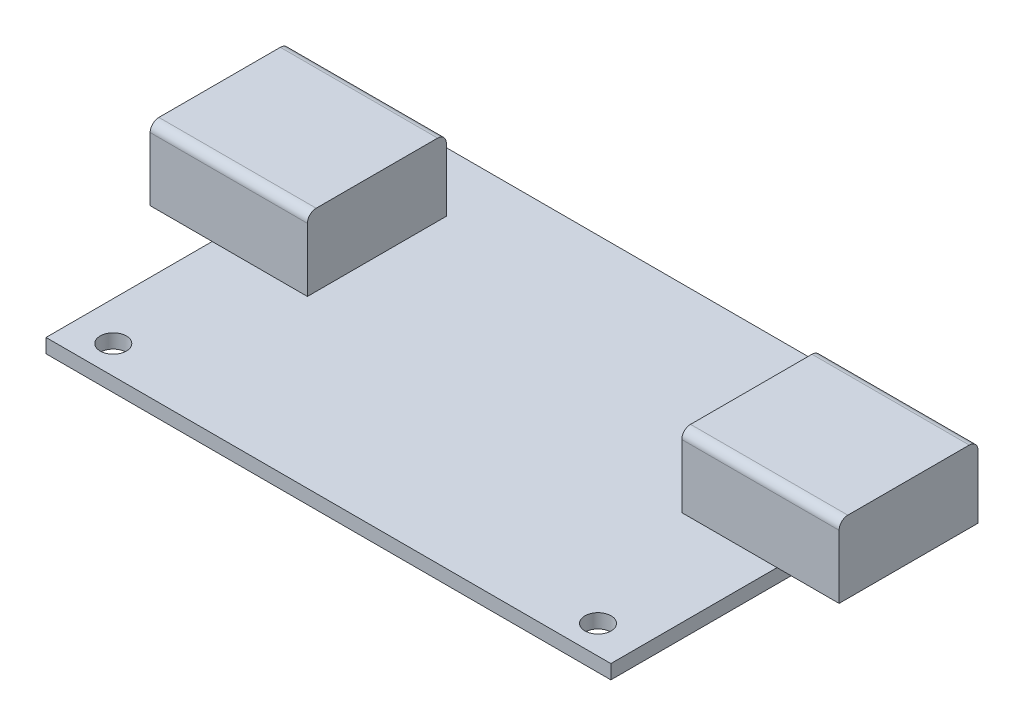
SolidWorks part; units mm, degrees
ref_plane "Front Plane" through (0, 0, 0) normal (0, 0, 1) x (1, 0, 0)
ref_plane "Top Plane" through (0, 0, 0) normal (0, 1, 0) x (1, 0, 0)
ref_plane "Right Plane" through (0, 0, 0) normal (1, 0, 0) x (0, 0, -1)
sketch "Sketch1" plane through (0, 0, 0) normal (0, 1, 0) x (1, 0, 0)
  line L0 (-27.875, -17.61) -> (27.605, -17.61) construction
  line L1 (-32.325, -20.86) -> (32.325, -20.86)
  line L2 (-32.325, -20.86) -> (-32.325, 20.86)
  line L3 (-32.325, 20.86) -> (32.325, 20.86)
  line L4 (32.325, -20.86) -> (32.325, 20.86)
  line L5 (-32.325, -20.86) -> (32.325, 20.86) construction
  line L6 (-32.325, 20.86) -> (32.325, -20.86) construction
  line L7 (-29.325, 17.01) -> (28.875, 17.01) construction
  circle A0 centre (27.605, -17.61) radius 1.5
  circle A1 centre (-27.875, -17.61) radius 1.5
  circle A2 centre (28.875, 17.01) radius 1.5
  circle A3 centre (-29.325, 17.01) radius 1.5
  point P0 (0, 0)
  dimension "D9" = 3
  dimension "D1" = 64.65
  dimension "D2" = 41.72
  dimension "D3" = 4.72
  dimension "D4" = 3.25
  dimension "D5" = 4.45
  dimension "D6" = 3.45
  dimension "D7" = 3
  dimension "D8" = 3.85
extrude "Boss-Extrude1" add sketch "Sketch1" along normal blind 1.62
sketch "Sketch2" plane through (0, 1.62, 0) normal (0, 1, 0) x (1, 0, 0)
  line L0 (32.325, 20.86) -> (-32.325, 20.86) construction
  line L1 (-39.425, -1.84) -> (-21.425, -1.84)
  line L2 (-39.425, -1.84) -> (-39.425, 14.06)
  line L3 (-39.425, 14.06) -> (-21.425, 14.06)
  line L4 (-21.425, -1.84) -> (-21.425, 14.06)
  line L5 (-39.425, -1.84) -> (-21.425, 14.06) construction
  line L6 (-39.425, 14.06) -> (-21.425, -1.84) construction
  line L7 (-32.325, 20.86) -> (-32.325, -20.86) construction
  point P0 (-30.425, 6.11)
  dimension "D1" = 6.8
  dimension "D2" = 15.9
  dimension "D3" = 10.9
  dimension "D4" = 18
extrude "Boss-Extrude2" add sketch "Sketch2" along normal blind 8.25
fillet "Fillet1" radius 1 2 edges at (-30.425, 9.87, -14.06) (-30.425, 9.87, 1.84)
mirror "Mirror1" about plane through (0, 0, 0) normal (1, 0, 0) of "Boss-Extrude2", "Fillet1"
